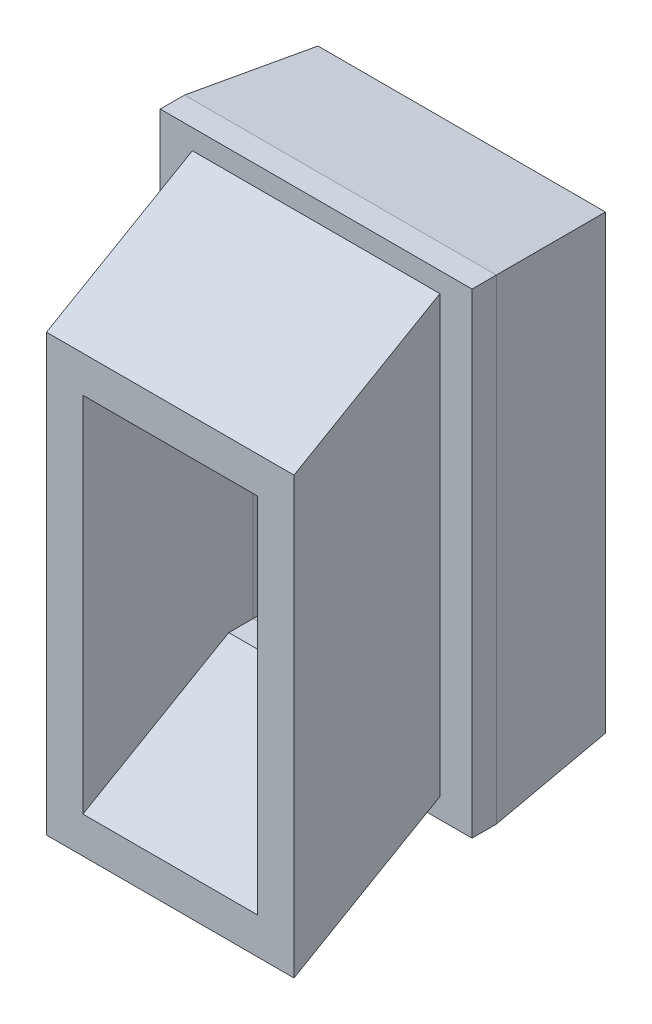
SolidWorks part; units mm, degrees
ref_plane "Front Plane" through (0, 0, 0) normal (0, 0, 1) x (1, 0, 0)
ref_plane "Top Plane" through (0, 0, 0) normal (0, 1, 0) x (1, 0, 0)
ref_plane "Right Plane" through (0, 0, 0) normal (1, 0, 0) x (0, 0, -1)
sketch "Sketch3" plane through (0, 0, 0) normal (0, 0, 1) x (1, 0, 0)
  line L1 (0, 0) -> (25.7, 0)
  line L2 (0, 0) -> (0, 39.2)
  line L3 (0, 39.2) -> (25.7, 39.2)
  line L4 (25.7, 0) -> (25.7, 39.2)
  line L5 (5.65, 4.65) -> (20.05, 4.65)
  line L6 (5.65, 4.65) -> (5.65, 34.55)
  line L7 (5.65, 34.55) -> (20.05, 34.55)
  line L8 (20.05, 4.65) -> (20.05, 34.55)
  point P9 (12.85, 34.55)
  point P10 (12.85, 39.2)
  point P11 (5.65, 19.6)
  point P12 (0, 19.6)
  dimension "D1" = 25.7
  dimension "D2" = 39.2
  dimension "D3" = 14.4
  dimension "D4" = 29.9
extrude "Boss-Extrude2" add sketch "Sketch3" along normal blind 12
chamfer "Chamfer1" distance 1 distance2 10 8 edges at (25.7, 19.6, 0) (12.85, 39.2, 0) (0, 19.6, 0) (12.85, 0, 0) (12.85, 4.65, 0) (20.05, 19.6, 0) (12.85, 34.55, 0) (5.65, 19.6, 0)
sketch "Sketch4" plane through (0, 0, 12) normal (0, 0, 1) x (1, 0, 0)
  line L0 (5.65, 4.65) -> (5.65, 34.55)
  line L1 (2.65, 37.55) -> (23.05, 37.55)
  line L3 (2.65, 1.65) -> (23.05, 1.65)
  line L4 (2.65, 1.65) -> (2.65, 37.55)
  line L5 (5.65, 34.55) -> (20.05, 34.55)
  line L6 (23.05, 37.55) -> (23.05, 1.65)
  line L7 (20.05, 34.55) -> (20.05, 4.65)
  line L8 (20.05, 4.65) -> (5.65, 4.65)
  dimension "D1" = 3
  dimension "D2" = 3
  dimension "D3" = 3
  dimension "D4" = 3
ref_plane "Plane1" through (12.85, 0, 0) normal (-1, 0, 0) x (0, 0, 1)
sketch "Sketch6" plane through (12.85, 0, 0) normal (-1, 0, 0) x (0, 0, 1)
  line L0 (12, 1.65) -> (24.0243, -5.2922)
  line L3 (12, 37.55) -> (12, 1.65) construction
  line L4 (12, 1.65) -> (12, 37.55) construction
  line L5 (12, 0) -> (12, 39.2) construction
  dimension "D1" = 60
sweep "Sweep1" add profiles "Sketch4" path "Sketch6"
